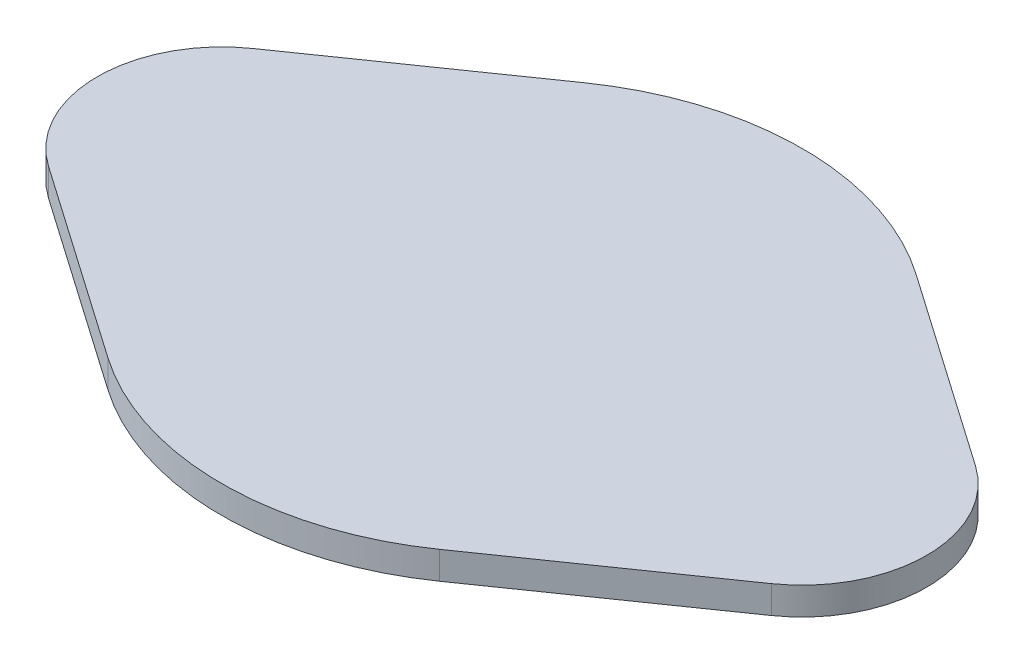
SolidWorks part; units mm, degrees
ref_plane "Front Plane" through (0, 0, 0) normal (0, 0, 1) x (1, 0, 0)
ref_plane "Top Plane" through (0, 0, 0) normal (0, 1, 0) x (1, 0, 0)
ref_plane "Right Plane" through (0, 0, 0) normal (1, 0, 0) x (0, 0, -1)
sketch "Sketch1" plane through (0, 0, 0) normal (0, 1, 0) x (1, 0, 0)
  line L0 (-30, 43.0842) -> (-65.3571, 18.4647)
  line L1 (-65.3571, -18.4647) -> (-30, -43.0842)
  line L2 (30, 43.0842) -> (65.3571, 18.4647)
  line L3 (65.3571, -18.4647) -> (30, -43.0842)
  arc A0 (-30, -43.0842) -> (30, -43.0842) centre (0, 0) ccw
  arc A1 (65.3571, -18.4647) -> (65.3571, 18.4647) centre (52.5, 0) ccw
  arc A2 (-65.3571, 18.4647) -> (-65.3571, -18.4647) centre (-52.5, 0) ccw
  arc A3 (30, 43.0842) -> (-30, 43.0842) centre (0, 0) ccw
  dimension "D1" = 45
  dimension "D2" = 105
extrude "Boss-Extrude1" add sketch "Sketch1" along normal blind 5
